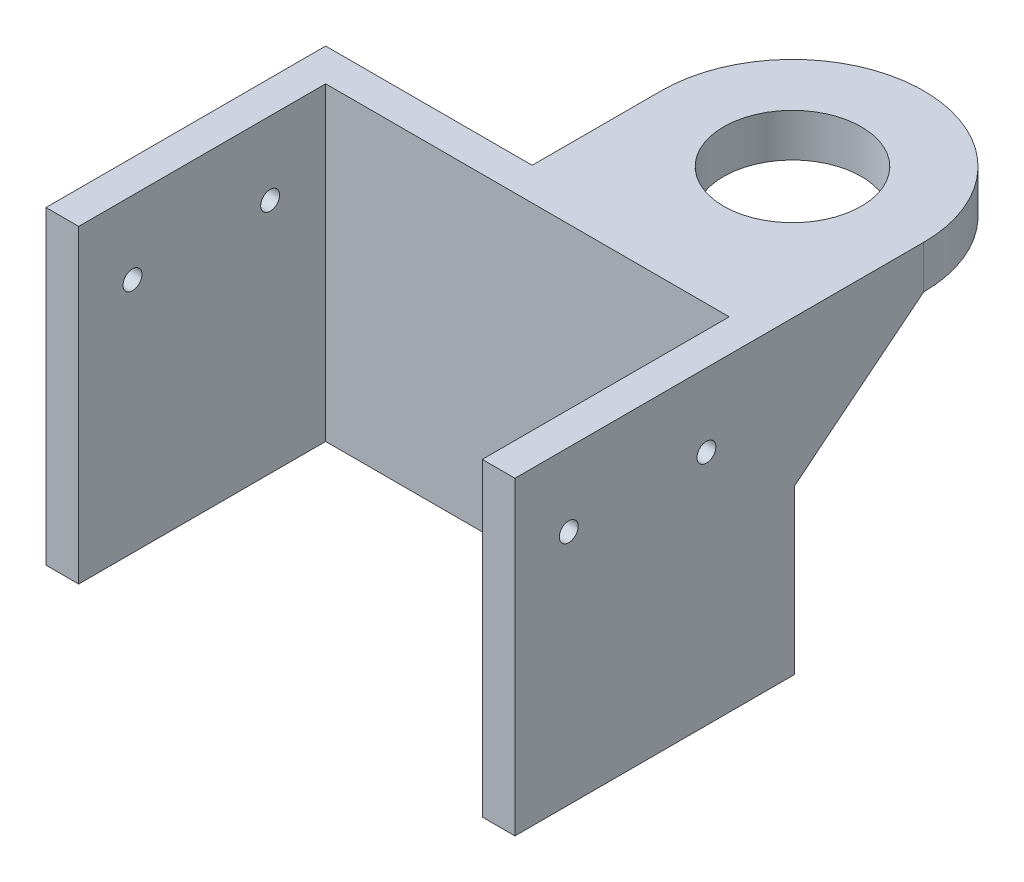
SolidWorks part; units mm, degrees
ref_plane "前视基准面" through (0, 0, 0) normal (0, 0, 1) x (1, 0, 0)
ref_plane "上视基准面" through (0, 0, 0) normal (0, 1, 0) x (1, 0, 0)
ref_plane "右视基准面" through (0, 0, 0) normal (1, 0, 0) x (0, 0, -1)
sketch "草图1" plane through (0, 0, 0) normal (0, 1, 0) x (1, 0, 0)
  line L1 (-22.7158, 19.8851) -> (31.7842, 19.8851)
  line L2 (-22.7158, 19.8851) -> (-22.7158, -12.6149)
  line L3 (-22.7158, -12.6149) -> (31.7842, -12.6149)
  line L4 (31.7842, 19.8851) -> (31.7842, -12.6149)
  dimension "D1" = 54.5
  dimension "D2" = 32.5
extrude "凸台-拉伸2" add sketch "草图1" along normal blind 34
ref_plane "基准面1" through (0, 34, 0) normal (0, 1, 0) x (1, 0, 0)
sketch "草图3" plane through (0, 34, 0) normal (0, 1, 0) x (1, 0, 0)
  line L0 (16.5342, 54.8716) -> (16.5342, -44.1047) construction
  line L1 (31.7842, -12.6149) -> (31.7842, 19.8851) construction
  line L2 (16.5342, 34.8851) -> (81.5256, 34.8851) construction
  line L3 (31.7842, 19.8851) -> (-22.7158, 19.8851) construction
  line L4 (1.2842, 34.8851) -> (1.2842, 19.8851)
  line L5 (31.7842, 34.8851) -> (31.7842, 19.8851)
  line L6 (1.2842, 19.8851) -> (31.7842, 19.8851)
  arc A0 (31.7842, 34.8851) -> (1.2842, 34.8851) centre (16.5342, 34.8851) ccw
  dimension "D2" = 30.5
  dimension "D1" = 15.25
  dimension "D3" = 15
extrude "凸台-拉伸3" add sketch "草图3" against normal blind 5
ref_plane "基准面6" through (1.2842, 0, 0) normal (-1, 0, 0) x (0, 0, 1)
sketch "草图11" plane through (1.2842, 0, 0) normal (-1, 0, 0) x (0, 0, 1)
  line L0 (-34.8851, 29) -> (-19.8851, 17)
  line L1 (-19.8851, 34) -> (-19.8851, 0) construction
  line L2 (-19.8851, 17) -> (-19.8851, 29)
  line L3 (-19.8851, 29) -> (-34.8851, 29)
extrude "凸台-拉伸6" add sketch "草图11" against normal blind 4
sketch "草图12" plane through (0, 34, 0) normal (0, 1, 0) x (1, 0, 0)
  line L0 (-73.5923, 38.2118) -> (93.7719, 38.2118) construction
ref_plane "基准面7" through (16.5342, 0, 0) normal (-1, 0, 0) x (0, 0, 1)
mirror "镜向1" about plane through (16.5342, 0, 0) normal (-1, 0, 0) of "凸台-拉伸6", "凸台-拉伸3"
sketch "草图14" plane through (0, 34, 0) normal (0, 1, 0) x (1, 0, 0)
  line L0 (-22.7158, -12.6149) -> (31.7842, -12.6149) construction
  line L1 (-18.9158, -12.6149) -> (27.9842, -12.6149)
  line L2 (-18.9158, -12.6149) -> (-18.9158, 16.0851)
  line L3 (-18.9158, 16.0851) -> (27.9842, 16.0851)
  line L4 (27.9842, -12.6149) -> (27.9842, 16.0851)
  line L5 (-22.7158, 19.8851) -> (-22.7158, -12.6149) construction
  line L6 (31.7842, -12.6149) -> (31.7842, 34.8851) construction
  line L7 (1.2842, 19.8851) -> (-22.7158, 19.8851) construction
  dimension "D1" = 3.8
  dimension "D2" = 3.8
  dimension "D3" = 3.8
extrude "切除-拉伸6" cut sketch "草图14" against normal through all
sketch "草图15" plane through (16.5342, 0, 0) normal (-1, 0, 0) x (0, 0, 1)
  line L0 (6.3649, 54.9892) -> (6.3649, -1.759) construction
  line L1 (12.6149, 34) -> (12.6149, 0) construction
  line L2 (-9.6351, 54.9892) -> (-9.6351, -1.759) construction
  line L3 (-19.8851, 17) -> (-19.8851, 34) construction
  line L4 (-9.6351, 25.5) -> (6.3649, 25.5) construction
  line L5 (-19.8851, 34) -> (12.6149, 34) construction
  circle A0 centre (-9.6351, 25.5) radius 1.1
  circle A1 centre (6.3649, 25.5) radius 1.1
  dimension "D4" = 2.2
  dimension "D5" = 2.2
  dimension "D1" = 6.25
  dimension "D2" = 10.25
  dimension "D3" = 8.5
extrude "切除-拉伸7" cut sketch "草图15" against normal mid plane 94
sketch "草图17" plane through (0, 0, 0) normal (0, 1, 0) x (1, 0, 0)
  line L0 (-22.7158, -12.6149) -> (-22.7158, 19.8851)
  line L1 (-22.7158, 19.8851) -> (31.7842, 19.8851)
  line L2 (31.7842, 19.8851) -> (31.7842, -12.6149)
  line L3 (31.7842, -12.6149) -> (27.9842, -12.6149)
  line L4 (27.9842, -12.6149) -> (27.9842, 16.0851)
  line L5 (27.9842, 16.0851) -> (-18.9158, 16.0851)
  line L6 (-18.9158, 16.0851) -> (-18.9158, -12.6149)
  line L7 (-18.9158, -12.6149) -> (-22.7158, -12.6149)
extrude "凸台-拉伸7" add sketch "草图17" against normal blind 2
sketch "草图18" plane through (0, 34, 0) normal (0, 1, 0) x (1, 0, 0)
  line L0 (1.2842, 34.8851) -> (60.5681, 34.8851) construction
  line L1 (16.5342, 22.4853) -> (16.5342, 64.1988) construction
  circle A0 centre (16.5342, 34.8851) radius 8
  dimension "D1" = 16
extrude "切除-拉伸8" cut sketch "草图18" against normal blind 10
sketch "草图19" plane through (0, -2, 0) normal (0, -1, 0) x (1, 0, 0)
  line L0 (37.2198, -17.8851) -> (-30.0251, -17.8851) construction
  line L1 (-20.7158, 17.2302) -> (-20.7158, -28.6671) construction
  line L2 (29.7842, 17.2302) -> (29.7842, -25.9986) construction
  line L3 (31.7842, -19.8851) -> (-22.7158, -19.8851) construction
  line L4 (31.7842, 12.6149) -> (31.7842, -19.8851) construction
  line L5 (-22.7158, -19.8851) -> (-22.7158, 12.6149) construction
  circle A0 centre (29.7842, -17.8851) radius 1
  circle A1 centre (-20.7158, -17.8851) radius 1
  dimension "D4" = 2
  dimension "D5" = 2
  dimension "D1" = 2
  dimension "D2" = 2
  dimension "D3" = 2
extrude "切除-拉伸9" cut sketch "草图19" against normal blind 20
